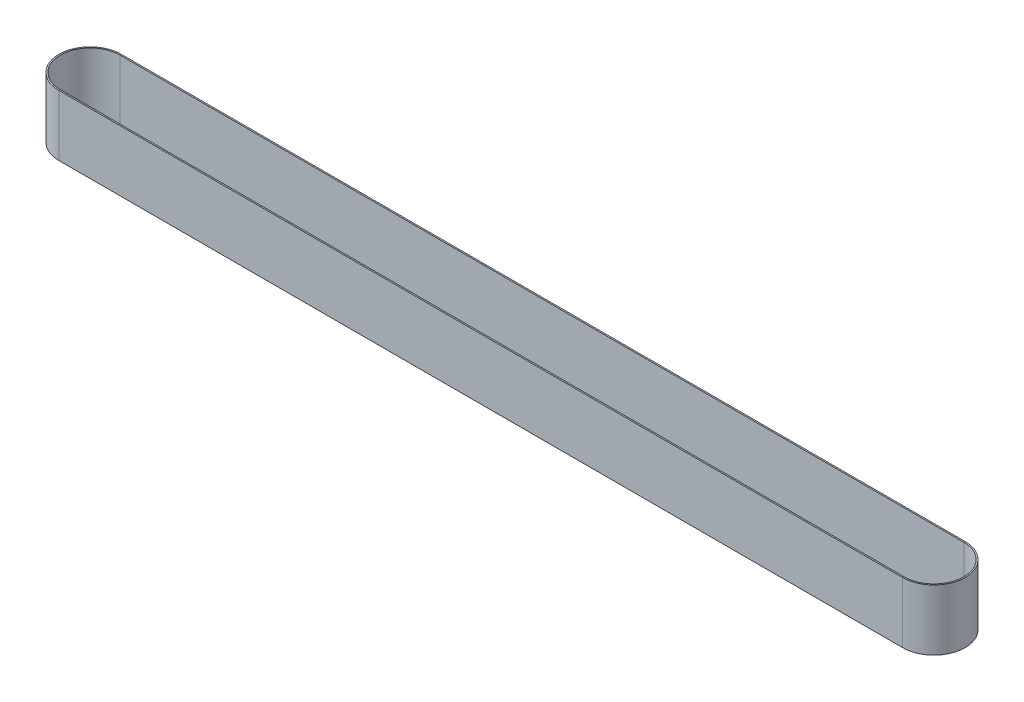
SolidWorks part; units mm, degrees
ref_plane "Front Plane" through (0, 0, 0) normal (0, 0, 1) x (1, 0, 0)
ref_plane "Top Plane" through (0, 0, 0) normal (0, 1, 0) x (1, 0, 0)
ref_plane "Right Plane" through (0, 0, 0) normal (1, 0, 0) x (0, 0, -1)
sketch "Sketch1" plane through (0, 0, 0) normal (0, 1, 0) x (1, 0, 0)
  line L0 (0, 0) -> (635, 0) construction
  line L1 (0, 23.5) -> (635, 23.5)
  line L2 (0, -23.5) -> (635, -23.5)
  line L3 (0, 0) -> (635, 0) construction
  line L4 (0, 22.5) -> (635, 22.5)
  line L5 (0, -22.5) -> (635, -22.5)
  arc A0 (0, 23.5) -> (0, -23.5) centre (0, 0) ccw
  arc A1 (635, -23.5) -> (635, 23.5) centre (635, 0) ccw
  arc A2 (0, 22.5) -> (0, -22.5) centre (0, 0) ccw
  arc A3 (635, -22.5) -> (635, 22.5) centre (635, 0) ccw
  point P3 (317.5, 0)
  point P10 (317.5, 0)
  dimension "D1" = 635
extrude "Boss-Extrude1" add sketch "Sketch1" along normal blind 45.72
